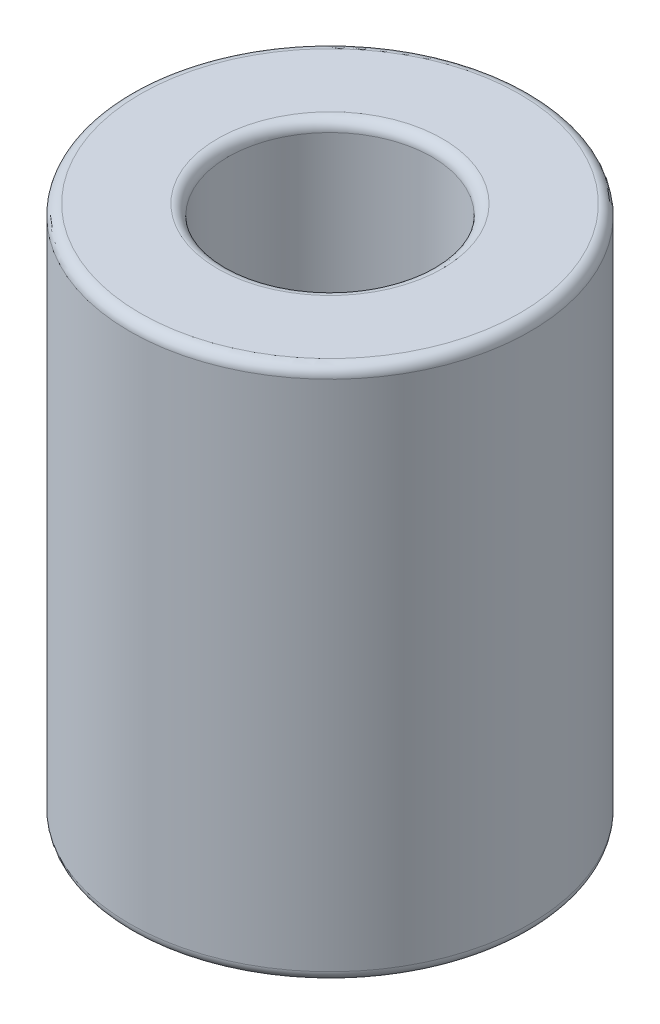
SolidWorks part; units mm, degrees
material "6061-T6 (SS)"
ref_plane "Plan de face" through (0, 0, 0) normal (0, 0, 1) x (1, 0, 0)
ref_plane "Plan de dessus" through (0, 0, 0) normal (0, 1, 0) x (1, 0, 0)
ref_plane "Plan de droite" through (0, 0, 0) normal (1, 0, 0) x (0, 0, -1)
sketch "Esquisse2" plane through (0, 0, 0) normal (0, 1, 0) x (1, 0, 0)
  circle A0 centre (0, 0) radius 9.525
  circle A1 centre (0, 0) radius 4.8514
  dimension "D1" = 19.05
  dimension "D2" = 9.7028
extrude "Boss.-Extru.1" add sketch "Esquisse2" along normal mid plane 25.4
fillet "Congé2" radius 0.5 4 edges at (0, -12.7, 4.8514) (0, -12.7, 9.525) (0, 12.7, 4.8514) (0, 12.7, 9.525)
equation "\"LENGHT\"=25.4"
equation "\"D1@Boss.-Extru.1\"=\"LENGHT\""
equation "\"OD\"=19.05"
equation "\"D1@Esquisse2\"=\"OD\""
equation "\"ID\"=9.7028"
equation "\"D2@Esquisse2\"=\"ID\""
